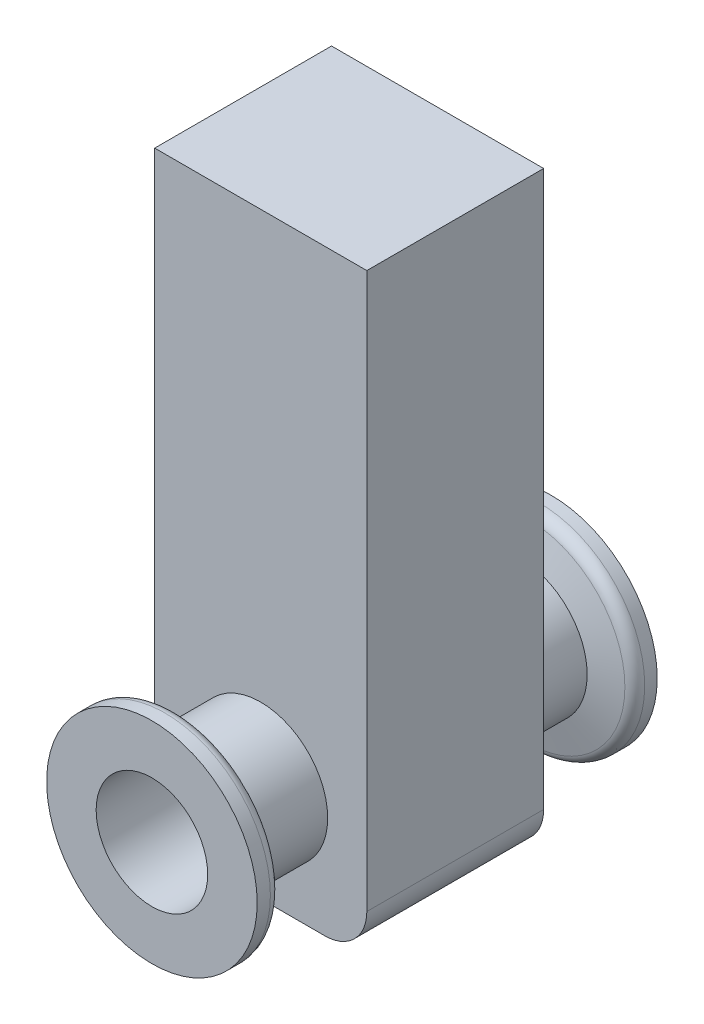
SolidWorks part; units mm, degrees
ref_plane "Front Plane" through (0, 0, 0) normal (0, 0, 1) x (1, 0, 0)
ref_plane "Top Plane" through (0, 0, 0) normal (0, 1, 0) x (1, 0, 0)
ref_plane "Right Plane" through (0, 0, 0) normal (1, 0, 0) x (0, 0, -1)
ref_plane "Plane1" through (0, 0, 12.5857) normal (0, 0, 1) x (1, 0, 0)
sketch "Sketch1" plane through (0, 0, 12.5857) normal (0, 0, 1) x (1, 0, 0)
  line L0 (-15.0968, 70.2714) -> (-15.0968, -8.7451)
  line L1 (-9.1133, -14.7286) -> (9.1133, -14.7286)
  line L2 (15.0968, -8.7451) -> (15.0968, 70.2714)
  line L3 (15.0968, 70.2714) -> (-15.0968, 70.2714)
  arc A0 (-15.0968, -8.7451) -> (-9.1133, -14.7286) centre (-9.1133, -8.7451) ccw
  arc A1 (9.1133, -14.7286) -> (15.0968, -8.7451) centre (9.1133, -8.7451) ccw
  dimension "D1" = 85
extrude "Boss-Extrude1" add sketch "Sketch1" against normal blind 25.1714
sketch "Sketch2" plane through (0, 0, 0) normal (0, 1, 0) x (1, 0, 0)
  line L0 (15.7677, 28.0797) -> (0.7407, 28.0797)
  line L1 (0.7407, 28.0797) -> (0.7407, 12.5857)
  line L2 (0.7407, 12.5857) -> (10.3067, 12.5857)
  line L3 (15.0968, 12.5857) -> (-15.0968, 12.5857) construction
  line L5 (10.3067, 12.5857) -> (10.3067, 23.5684)
  line L6 (10.3067, 23.5684) -> (14.544, 24.7038)
  line L7 (15.7677, 26.2986) -> (15.7677, 28.0797)
  line L8 (0.7407, 28.0797) -> (0.7407, 12.5857) construction
  arc A0 (14.544, 24.7038) -> (15.7677, 26.2986) centre (14.1167, 26.2986) ccw
  point P3 (0, 0)
revolve "Revolve1" add sketch "Sketch2" angle 360 about L8
sketch "Sketch3" plane through (0, 0, 0) normal (0, 1, 0) x (1, 0, 0)
  line L0 (9.525, -12.5857) -> (0, -12.5857)
  line L1 (0, -12.5857) -> (0, -28.0797)
  line L2 (0, -28.0797) -> (14.986, -28.0797)
  line L3 (14.986, -28.0797) -> (14.986, -26.2011)
  line L4 (13.8564, -24.729) -> (9.525, -23.5684)
  line L5 (9.525, -23.5684) -> (9.525, -12.5857)
  line L6 (15.0968, -12.5857) -> (-15.0968, -12.5857) construction
  line L8 (0, -3.0607) -> (0, -28.0797) construction
  arc A0 (14.986, -26.2011) -> (13.8564, -24.729) centre (13.462, -26.2011) ccw
  point P11 (0, 0)
revolve "Revolve2" add sketch "Sketch3" angle 360 about L8
ref_plane "Plane2" through (0, 0, 0) normal (0, -1, 0) x (1, 0, 0)
sketch "Sketch4" plane through (0, 0, 0) normal (0, -1, 0) x (1, 0, 0)
  line L0 (8.636, 37.6047) -> (0, 37.6047)
  line L1 (0, 37.6047) -> (0, -37.6047)
  line L2 (0, -37.6047) -> (8.636, -37.6047)
  line L3 (8.636, -37.6047) -> (8.636, -35.0647)
  line L4 (8.636, -35.0647) -> (7.9375, -35.0647)
  line L5 (7.9375, -35.0647) -> (7.9375, 35.0647)
  line L6 (7.9375, 35.0647) -> (8.636, 35.0647)
  line L7 (8.636, 35.0647) -> (8.636, 37.6047)
  line L8 (0, 37.6047) -> (0, -37.6047) construction
revolve "Cut-Revolve1" cut sketch "Sketch4" angle 360 about L8
